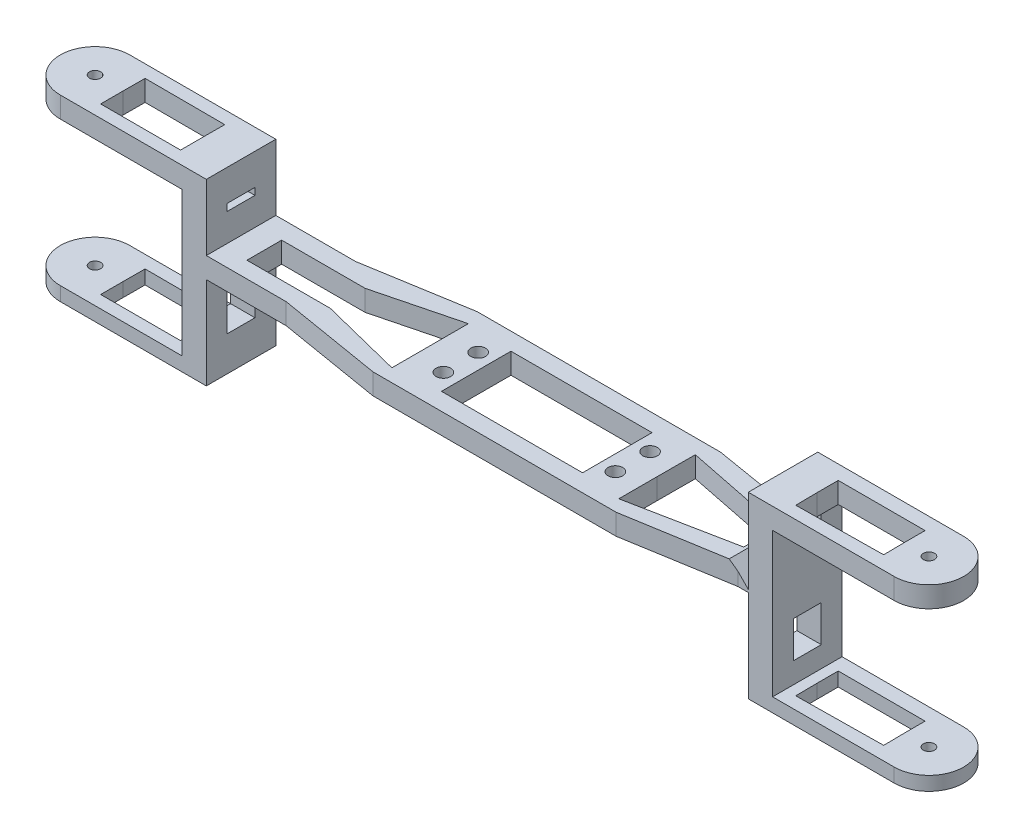
SolidWorks part; units mm, degrees
ref_plane "前视基准面" through (0, 0, 0) normal (0, 0, 1) x (1, 0, 0)
ref_plane "上视基准面" through (0, 0, 0) normal (0, 1, 0) x (1, 0, 0)
ref_plane "右视基准面" through (0, 0, 0) normal (1, 0, 0) x (0, 0, -1)
sketch "草图1" plane through (0, 0, 0) normal (0, 1, 0) x (1, 0, 0)
  line L0 (-42.06, 15.3245) -> (27.94, 15.3245)
  line L1 (-27.36, 10.3245) -> (13.24, 10.3245)
  line L3 (-27.36, -9.6755) -> (13.24, -9.6755)
  line L5 (27.94, 15.3245) -> (27.94, -14.6755)
  line L6 (27.94, -14.6755) -> (-42.06, -14.6755)
  line L7 (-42.06, -14.6755) -> (-42.06, 15.3245)
  line L8 (-7.06, 15.3245) -> (-7.06, -14.6755) construction
  line L9 (-42.06, 0.3245) -> (27.94, 0.3245) construction
  line L10 (13.24, 10.3245) -> (13.24, -9.6755)
  line L11 (-27.36, 10.3245) -> (-27.36, -9.6755)
  dimension "D1" = 20.3
  dimension "D5" = 5
  dimension "D6" = 5
extrude "凸台-拉伸1" add sketch "草图1" along normal blind 51.5
sketch "草图2" plane through (0, 51.5, 0) normal (0, 1, 0) x (1, 0, 0)
  line L0 (-42.06, 0.3245) -> (27.94, 0.3245) construction
  line L1 (-42.06, 15.3245) -> (-42.06, -14.6755) construction
  line L2 (27.94, -14.6755) -> (27.94, 15.3245) construction
  line L3 (-7.06, 15.3245) -> (-7.06, -14.6755) construction
  line L4 (27.94, 15.3245) -> (-42.06, 15.3245) construction
  line L5 (-42.06, -14.6755) -> (27.94, -14.6755) construction
  circle A0 centre (-31.81, 5.3245) radius 2.1
  circle A1 centre (-31.81, -4.6755) radius 2.1
  circle A2 centre (17.69, -4.6755) radius 2.1
  circle A3 centre (17.69, 5.3245) radius 2.1
  dimension "D1" = 24.75
  dimension "D2" = 5
extrude "切除-拉伸1" cut sketch "草图2" against normal through all
sketch "草图3" plane through (0, 51.5, 0) normal (0, 1, 0) x (1, 0, 0)
  line L0 (-7.06, 15.3245) -> (-7.06, -14.6755) construction
  line L1 (27.94, 15.3245) -> (-42.06, 15.3245) construction
  line L2 (-42.06, -14.6755) -> (27.94, -14.6755) construction
  line L3 (-42.06, 0.3245) -> (27.94, 0.3245) construction
  line L4 (-42.06, 15.3245) -> (-42.06, -14.6755) construction
  line L5 (27.94, -14.6755) -> (27.94, 15.3245) construction
  line L6 (-137.06, 10.3245) -> (-72.06, 10.3245)
  line L7 (-72.06, 10.3245) -> (-42.06, 15.3245)
  line L8 (-42.06, 15.3245) -> (-42.06, -14.6755)
  line L9 (-72.06, -9.6755) -> (-42.06, -14.6755)
  line L10 (-137.06, -9.6755) -> (-72.06, -9.6755)
  line L11 (-137.06, 10.3245) -> (-137.06, -9.6755) construction
  line L12 (-17.06, 10.3245) -> (-17.06, -9.6755) construction
  line L13 (13.24, 10.3245) -> (-27.36, 10.3245) construction
  line L14 (-27.36, -9.6755) -> (13.24, -9.6755) construction
  line L16 (57.94, 10.3245) -> (102.94, 10.3245)
  line L18 (57.94, -9.6755) -> (27.94, -14.6755)
  line L19 (27.94, 15.3245) -> (27.94, -14.6755)
  line L20 (57.94, 10.3245) -> (27.94, 15.3245)
  line L22 (57.94, -9.6755) -> (102.94, -9.6755)
  line L23 (102.94, 10.3245) -> (102.94, -9.6755) construction
  arc A2 (-137.06, 10.3245) -> (-137.06, -9.6755) centre (-137.06, 0.3245) ccw
  circle A3 centre (-137.06, 0.3245) radius 1.6
  arc A4 (102.94, -9.6755) -> (102.94, 10.3245) centre (102.94, 0.3245) ccw
  circle A6 centre (102.94, 0.3245) radius 1.6
  dimension "D1" = 10
  dimension "D2" = 30
  dimension "D3" = 65
  dimension "D4" = 35
  dimension "D6" = 25
  dimension "D7" = 45
extrude "凸台-拉伸2" add sketch "草图3" against normal blind 51.5
sketch "草图17" plane through (0, 0, 14.6755) normal (0, 0, 1) x (1, 0, 0)
  line L0 (112.94, 45.5) -> (67.94, 45.5)
  line L1 (-137.06, 51.5) -> (-72.06, 51.5) construction
  line L2 (112.94, 0) -> (112.94, 51.5) construction
  line L3 (67.94, 45.5) -> (67.94, 4)
  line L4 (-137.06, 0) -> (-72.06, 0) construction
  line L5 (67.94, 4) -> (112.94, 4)
  line L6 (112.94, 51.5) -> (102.94, 51.5) construction
  line L7 (-147.0346, 45.5) -> (-117.0346, 45.5)
  line L9 (-117.0346, 4) -> (-147.06, 4)
  line L11 (-95.0346, 34.5) -> (60.94, 34.5)
  line L12 (57.94, 0) -> (102.94, 0) construction
  line L14 (60.94, 51.5) -> (60.94, 34.5)
  line L15 (57.94, 51.5) -> (102.94, 51.5) construction
  line L16 (-42.06, 51.5) -> (27.94, 51.5) construction
  line L18 (-95.0346, 51.5) -> (60.94, 51.5)
  line L19 (-95.0346, 0) -> (60.94, 0)
  line L21 (60.94, 26.5) -> (60.94, 0)
  line L23 (-147.0346, 45.5) -> (-149.5831, 45.5)
  line L24 (-149.5831, 45.5) -> (-149.5831, 4)
  line L25 (-149.5831, 4) -> (-147.06, 4)
  line L26 (112.94, 45.5) -> (117.1014, 45.5)
  line L27 (117.1014, 45.5) -> (117.1014, 4)
  line L28 (117.1014, 4) -> (112.94, 4)
  line L29 (-102.06, 25.5) -> (-102.06, 4)
  line L31 (-95.0346, 26.5) -> (-95.0346, 0)
  line L32 (-95.0346, 51.5) -> (-95.0346, 34.5)
  line L33 (-117.0346, 45.5) -> (-102.06, 45.5)
  line L34 (-117.0346, 4) -> (-102.06, 4)
  line L35 (-95.0346, 26.5) -> (60.94, 26.5)
  line L36 (-147.06, 51.5) -> (-147.06, 0) construction
  line L37 (-102.06, 25.5) -> (-102.06, 45.5)
  point P24 (-102.06, 35.5)
  dimension "D1" = 45
  dimension "D2" = 6
  dimension "D3" = 4
  dimension "D4" = 6
  dimension "D5" = 4
  dimension "D6" = 45
  dimension "D8" = 17
  dimension "D10" = 21.5
extrude "切除-拉伸8" cut sketch "草图17" against normal through all
sketch "草图18" plane through (0, 0, 0) normal (0, -1, 0) x (1, 0, 0)
  line L0 (60.94, 0) -> (112.94, -0.3245) construction
  line L1 (60.94, -10.3245) -> (60.94, 9.6755) construction
  line L2 (70.94, -6.2137) -> (70.94, -0.0624)
  line L3 (70.94, -6.2137) -> (95.94, -6.2137)
  line L4 (95.94, -6.2137) -> (95.94, -0.2184)
  line L5 (96.0148, 5.7765) -> (95.94, -0.2184)
  line L6 (71.0168, 6.0885) -> (96.0148, 5.7765)
  line L7 (71.0168, 6.0885) -> (70.94, -0.0624)
  line L8 (-64.0346, 4.9906) -> (-88.0346, 4.9906)
  line L9 (54.94, -0.0094) -> (54.94, 4.9906)
  line L10 (54.94, 4.9906) -> (24.94, 10.9438)
  line L11 (24.94, 10.9438) -> (24.94, -0.0562)
  line L12 (24.9743, -11.0561) -> (24.94, -0.0562)
  line L13 (54.9556, -5.0093) -> (24.9743, -11.0561)
  line L14 (54.94, -0.0094) -> (54.9556, -5.0093)
  line L15 (-106.0346, 6.0885) -> (-106.0346, -0.2605)
  line L16 (-106.0346, 6.0885) -> (-129.0346, 6.0885)
  line L17 (-129.0346, 6.0885) -> (-129.0346, -0.2964)
  line L18 (-95.0346, -10.3245) -> (-95.0346, 9.6755) construction
  line L19 (-129.0146, -6.6812) -> (-129.0346, -0.2964)
  line L20 (-106.0147, -6.6094) -> (-129.0146, -6.6812)
  line L21 (-106.0147, -6.6094) -> (-106.0346, -0.2605)
  line L24 (-40.36, 10.9438) -> (-40.36, -11.0561)
  line L25 (-40.36, -11.0561) -> (-64.0346, -5.0093)
  line L26 (-64.0346, -5.0093) -> (-88.0346, -5.0093)
  line L27 (-88.0346, -5.0093) -> (-88.0346, 4.9906)
  line L28 (-27.36, -10.3245) -> (-27.36, 9.6755) construction
  line L29 (-64.0346, 4.9906) -> (-40.36, 10.9438)
  arc A0 (102.94, -10.3245) -> (102.94, 9.6755) centre (102.94, -0.3245) ccw construction
  dimension "D1" = 25
  dimension "D2" = 10
  dimension "D3" = 5
  dimension "D4" = 11
  dimension "D5" = 30
  dimension "D6" = 6
  dimension "D7" = 23
  dimension "D8" = 11
  dimension "D9" = 7
  dimension "D10" = 13
  dimension "D11" = 24
extrude "切除-拉伸9" cut sketch "草图18" against normal through all
sketch "草图20" plane through (-95.0346, 0, 0) normal (1, 0, 0) x (0, 0, -1)
  line L0 (0.3245, 51.5) -> (0.3245, -12.9945) construction
  line L1 (10.3245, 51.5) -> (-9.6755, 51.5) construction
  line L2 (10.3245, 4) -> (10.3245, 45.5) construction
  line L3 (-3.6755, 10) -> (4.3245, 10)
  line L4 (-3.6755, 10) -> (-3.6755, 20.5)
  line L5 (-3.6755, 20.5) -> (4.3245, 20.5)
  line L6 (4.3245, 10) -> (4.3245, 20.5)
  line L7 (10.3245, 26.5) -> (-9.6755, 26.5) construction
  line L8 (10.3245, 34.5) -> (10.3245, 51.5) construction
  line L9 (10.3245, 4) -> (-9.6755, 4) construction
  line L10 (4.3245, 40.5) -> (-3.6755, 40.5)
  line L11 (4.3245, 40.5) -> (4.3245, 42.5)
  line L12 (4.3245, 42.5) -> (-3.6755, 42.5)
  line L13 (-3.6755, 40.5) -> (-3.6755, 42.5)
  line L14 (4.3245, 40.5) -> (-3.6755, 42.5) construction
  line L15 (4.3245, 42.5) -> (-3.6755, 40.5) construction
  line L16 (10.3245, 34.5) -> (-9.6755, 34.5) construction
  point P4 (0.3245, 24.8576)
  point P15 (0.3245, 41.5)
  dimension "D1" = 6
  dimension "D2" = 6
  dimension "D3" = 6
  dimension "D4" = 6
  dimension "D5" = 6
  dimension "D6" = 2
extrude "切除-拉伸10" cut sketch "草图20" against normal through all and the other way through all
sketch "草图21" plane through (0, 0, -15.3245) normal (0, 0, -1) x (-1, 0, 0)
  line L0 (-55.8031, 32.5) -> (94.9247, 32.5)
  line L1 (95.0346, 26.5) -> (72.06, 26.5) construction
  line L2 (95.0346, 34.5) -> (95.0346, 32.5)
  line L3 (-60.94, 34.5) -> (88.0346, 34.5)
  line L6 (-60.94, 34.5) -> (-60.94, 27.3)
  line L7 (-37.7145, 27.3) -> (-31.7187, 27.3) construction
  line L8 (-60.94, 27.3) -> (-55.8031, 32.5)
  line L9 (88.0346, 34.5) -> (95.0346, 34.5)
  line L10 (95.0346, 32.5) -> (94.9247, 32.5)
  dimension "D1" = 6
extrude "切除-拉伸11" cut sketch "草图21" against normal through all
